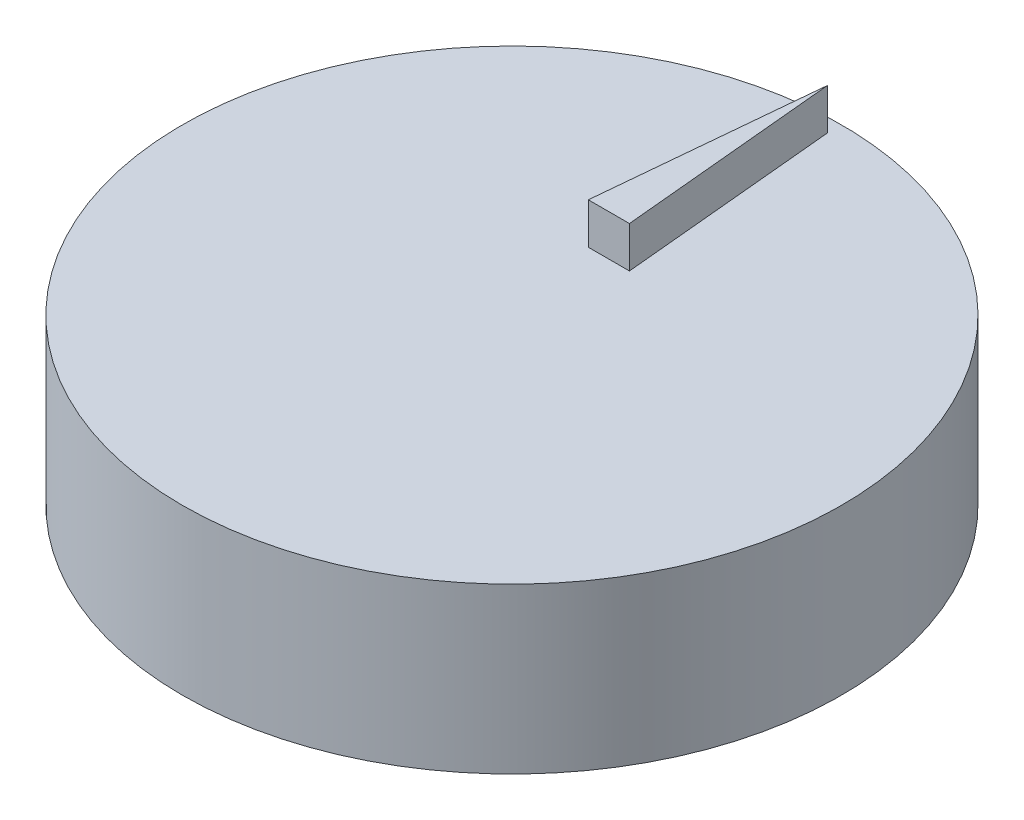
SolidWorks part; units mm, degrees
ref_plane "Front Plane" through (0, 0, 0) normal (0, 0, 1) x (1, 0, 0)
ref_plane "Top Plane" through (0, 0, 0) normal (0, 1, 0) x (1, 0, 0)
ref_plane "Right Plane" through (0, 0, 0) normal (1, 0, 0) x (0, 0, -1)
sketch "Sketch2" plane through (0, 0, 0) normal (0, 1, 0) x (1, 0, 0)
  circle A0 centre (0, 15) radius 40.0812
  dimension "D1" = 15
extrude "Boss-Extrude2" add sketch "Sketch2" along normal blind 20
sketch "Sketch1" plane through (0, 0, 0) normal (0, 1, 0) x (1, 0, 0)
  line L0 (-2.5, -3) -> (2.5, -3)
  line L1 (-2.5, -10) -> (2.5, -10)
  line L2 (-2.5, -10) -> (-2.5, -13)
  line L3 (-2.5, -13) -> (2.5, -13)
  line L4 (2.5, -10) -> (2.5, -13)
  line L5 (2.5, -3) -> (2.5, -6)
  line L6 (-2.5, -6) -> (2.5, -6)
  line L7 (-2.5, -3) -> (-2.5, -6)
  line L8 (-2.5, 4) -> (2.5, 4)
  line L9 (2.5, 4) -> (2.5, 1)
  line L10 (-2.5, 1) -> (2.5, 1)
  line L11 (-2.5, 4) -> (-2.5, 1)
  line L12 (-2.5, 11) -> (2.5, 11)
  line L13 (2.5, 11) -> (2.5, 8)
  line L14 (-2.5, 8) -> (2.5, 8)
  line L15 (-2.5, 11) -> (-2.5, 8)
  line L16 (-2.5, 18) -> (2.5, 18)
  line L17 (2.5, 18) -> (2.5, 15)
  line L18 (-2.5, 15) -> (2.5, 15)
  line L19 (-2.5, 18) -> (-2.5, 15)
  line L20 (-2.5, 25) -> (2.5, 25)
  line L21 (2.5, 25) -> (2.5, 22)
  line L22 (-2.5, 22) -> (2.5, 22)
  line L23 (-2.5, 25) -> (-2.5, 22)
  dimension "D1" = 5
  dimension "D2" = 3
  dimension "D3" = 2.5
  dimension "D4" = 10
  dimension "D5" = 6
extrude "Cut-Extrude1" cut sketch "Sketch1" along normal blind 8
sketch "Sketch3" plane through (0, 20, 0) normal (0, 1, 0) x (1, 0, 0)
  line L0 (0, 53.3674) -> (-2.5, 26.7902)
  line L1 (-2.5, 26.7902) -> (2.5, 26.7902)
  line L2 (2.5, 26.7902) -> (0, 53.3674)
  dimension "D1" = 5
  dimension "D2" = 2.5
  dimension "D3" = 0
extrude "Boss-Extrude3" add sketch "Sketch3" along normal blind 5
